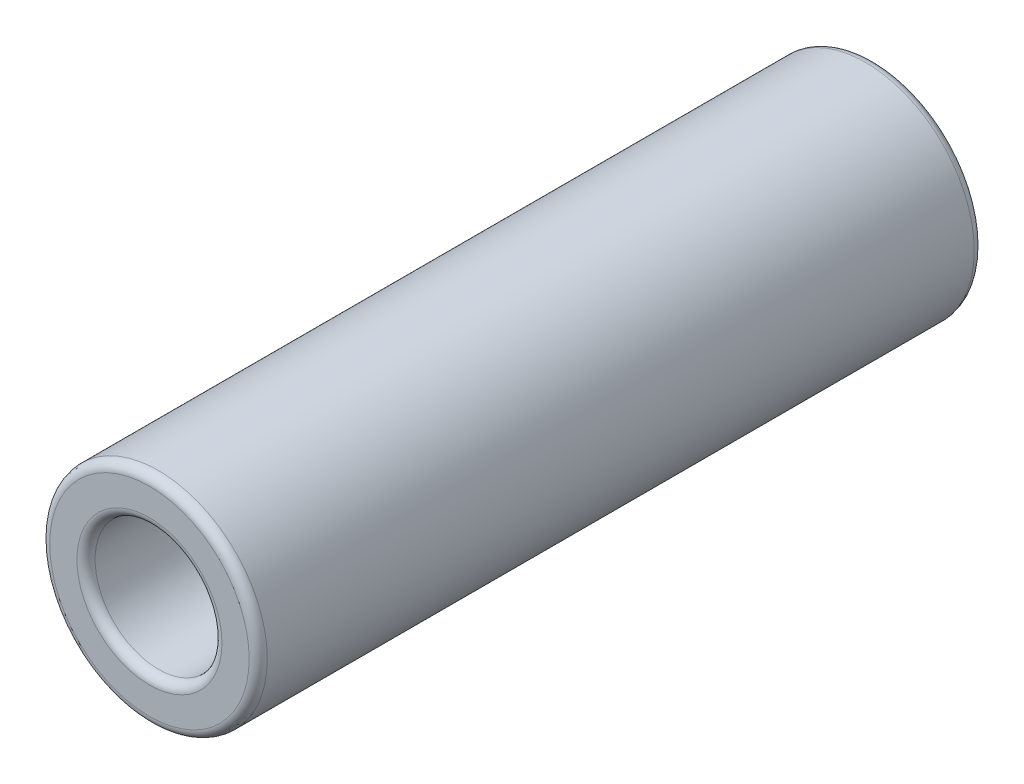
SolidWorks part; units mm, degrees
ref_plane "Płaszczyzna przednia" through (0, 0, 0) normal (0, 0, 1) x (1, 0, 0)
ref_plane "Płaszczyzna górna" through (0, 0, 0) normal (0, 1, 0) x (1, 0, 0)
ref_plane "Płaszczyzna prawa" through (0, 0, 0) normal (1, 0, 0) x (0, 0, -1)
sketch "Szkic1" plane through (0, 0, 0) normal (0, 0, 1) x (1, 0, 0)
  circle A0 centre (0, 0) radius 3.5
  circle A1 centre (0, 0) radius 6
  dimension "D1" = 7
  dimension "D2" = 12
extrude "Dodanie-wyciągnięcie1" add sketch "Szkic1" against normal blind 40
fillet "Zaokrąglenie1" radius 0.5 2 edges at (6, 0, -40) (6, 0, 0)
fillet "Zaokrąglenie2" radius 0.5 2 edges at (3.5, 0, -40) (3.5, 0, 0)
